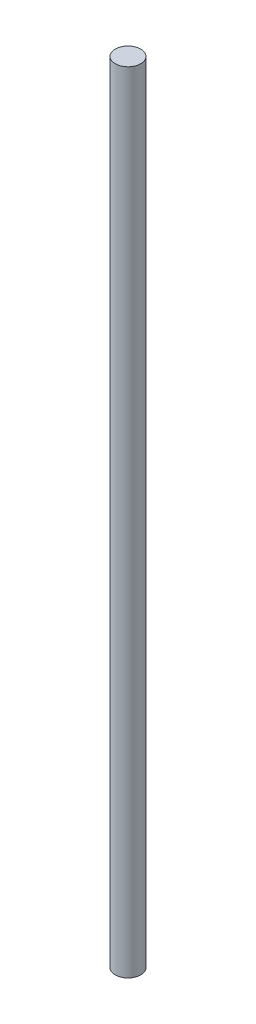
SolidWorks part; units mm, degrees
ref_plane "Front Plane" through (0, 0, 0) normal (0, 0, 1) x (1, 0, 0)
ref_plane "Top Plane" through (0, 0, 0) normal (0, 1, 0) x (1, 0, 0)
ref_plane "Right Plane" through (0, 0, 0) normal (1, 0, 0) x (0, 0, -1)
sketch "Sketch1" plane through (0, 0, 0) normal (0, 1, 0) x (1, 0, 0)
  circle A0 centre (0, 0) radius 3.175
  dimension "D1" = 6.35
extrude "Boss-Extrude1" add sketch "Sketch1" along normal blind 196.85
